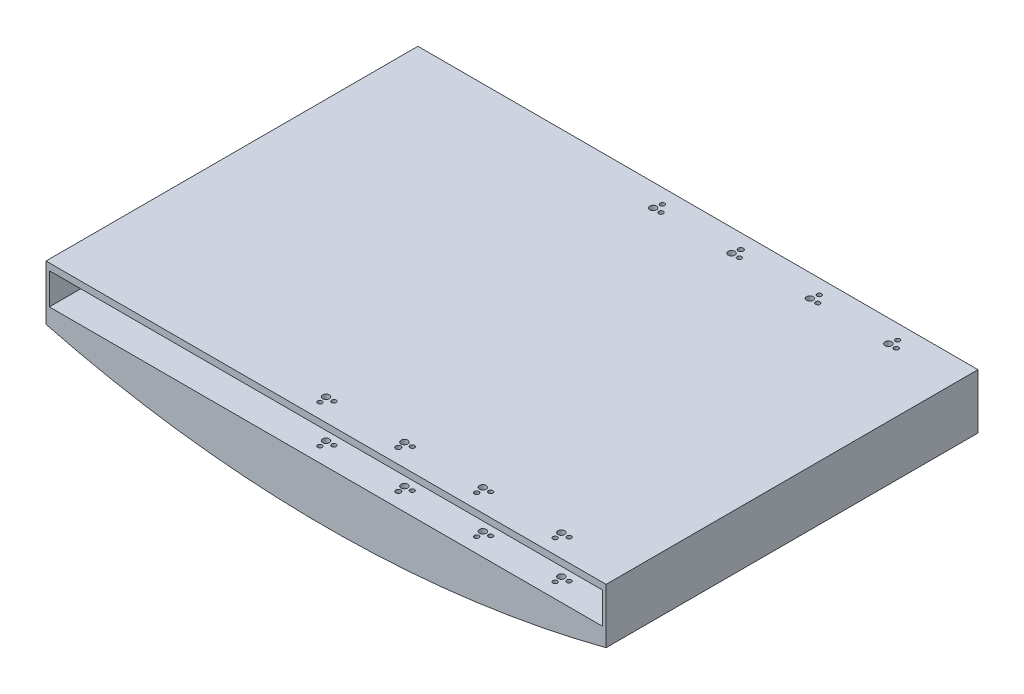
SolidWorks part; units mm, degrees
ref_plane "Front Plane" through (0, 0, 0) normal (0, 0, 1) x (1, 0, 0)
ref_plane "Top Plane" through (0, 0, 0) normal (0, 1, 0) x (1, 0, 0)
ref_plane "Right Plane" through (0, 0, 0) normal (1, 0, 0) x (0, 0, -1)
sketch "Sketch1" plane through (0, 0, 0) normal (0, 0, 1) x (1, 0, 0)
  line L2 (0, 0) -> (0, 49)
  line L3 (0, 49) -> (500, 49)
  line L4 (500, 0) -> (500, 49)
  line L9 (3, 45.5) -> (497, 45.5)
  line L10 (3, 45.5) -> (3, 12.5)
  line L11 (3, 12.5) -> (497, 12.5)
  line L12 (497, 45.5) -> (497, 12.5)
  arc A0 (0, 0) -> (500, 0) centre (250, 967.6003) ccw
  point P6 (250, -31.7747)
  dimension "D3" = 494
  dimension "D1" = 500
  dimension "D2" = 49
  dimension "D4" = 3
  dimension "D5" = 33
  dimension "D6" = 3.5
extrude "Boss-Extrude2" add sketch "Sketch1" along normal mid plane 332
sketch "Sketch6" plane through (0, 0, 0) normal (0, 0, 1) x (1, 0, 0)
  line L0 (3, 0) -> (497, 0)
  line L1 (3, 0) -> (3, -32.5581)
  line L2 (497, 0) -> (497, -32.5581)
  line L3 (3, -32.5581) -> (497, -32.5581)
  point P0 (497, 0)
  point P1 (3, 0)
extrude "Cut-Extrude2" cut sketch "Sketch6" against normal mid plane 312
sketch "Sketch7" plane through (0, 49, 0) normal (0, 1, 0) x (1, 0, 0)
  line L0 (500, -166) -> (0, -166) construction
  line L1 (0, -166) -> (0, 166) construction
  line L2 (230, -146) -> (231.3668, -152.8653) construction
  line L3 (300, -136.3) -> (300, -160.3273) construction
  line L4 (370, -134.9651) -> (370, -158.1025) construction
  line L5 (440, -134.9651) -> (440, -158.8911) construction
  line L6 (300, -146) -> (305.8829, -175.5484) construction
  line L7 (370, -146) -> (375.3706, -172.9753) construction
  line L8 (440, -146) -> (445.6513, -174.3852) construction
  line L10 (-44.4261, 0) -> (44.4261, 0) construction
  circle A0 centre (230, -146) radius 3
  circle A1 centre (300, -146) radius 3
  circle A2 centre (370, -146) radius 3
  circle A3 centre (440, -146) radius 3
  circle A8 centre (231.3668, -152.8653) radius 2
  circle A9 centre (301.3668, -152.8653) radius 2.2706
  circle A10 centre (371.3668, -152.8653) radius 2
  circle A11 centre (441.3668, -152.8653) radius 2
  circle A12 centre (237, -146) radius 2
  circle A13 centre (307, -146) radius 2
  circle A14 centre (377, -146) radius 2
  circle A15 centre (447, -146) radius 2
  circle A24 centre (440, 146) radius 3
  circle A25 centre (370, 146) radius 3
  circle A26 centre (300, 146) radius 3
  circle A27 centre (230, 146) radius 3
  circle A28 centre (441.3668, 152.8653) radius 2
  circle A29 centre (447, 146) radius 2
  circle A30 centre (371.3668, 152.8653) radius 2
  circle A31 centre (377, 146) radius 2
  circle A32 centre (307, 146) radius 2
  circle A33 centre (301.3668, 152.8653) radius 2.2706
  circle A34 centre (237, 146) radius 2
  circle A35 centre (231.3668, 152.8653) radius 2
  dimension "D1" = 6
  dimension "D2" = 6
  dimension "D3" = 6
  dimension "D4" = 6
  dimension "D10" = 4
  dimension "D18" = 4
  dimension "D19" = 4
  dimension "D21" = 4
  dimension "D22" = 4
  dimension "D25" = 4
  dimension "D26" = 4
  dimension "D5" = 20
  dimension "D6" = 230
  dimension "D7" = 70
  dimension "D8" = 70
  dimension "D9" = 70
  dimension "D11" = 7
  dimension "D12" = 11.26
  dimension "D13" = 11.26
  dimension "D14" = 11.26
  dimension "D15" = 7
  dimension "D16" = 7
  dimension "D17" = 7
  dimension "D20" = 7
  dimension "D23" = 7
  dimension "D24" = 7
  dimension "D27" = 7
sketch "Sketch8" plane through (0, 12.5, 0) normal (0, 1, 0) x (1, 0, 0)
  line L0 (3, -166) -> (497, -166)
  line L1 (3, -166) -> (3, -136)
  line L2 (497, -166) -> (497, -136)
  line L3 (3, -136) -> (497, -136)
  dimension "D1" = 30
extrude "Boss-Extrude3" add sketch "Sketch8" along normal blind 2.5
sketch "Sketch9" plane through (0, 45.5, 0) normal (0, -1, 0) x (1, 0, 0)
  line L0 (497, 166) -> (497, -166) construction
  line L1 (3, 166) -> (497, 166)
  line L2 (3, 166) -> (3, 136)
  line L3 (3, 136) -> (497, 136)
  line L4 (497, 166) -> (497, 136)
  dimension "D1" = 30
extrude "Boss-Extrude4" add sketch "Sketch9" along normal blind 2.5
sketch "Sketch10" plane through (0, 45.5, 0) normal (0, -1, 0) x (1, 0, 0)
  line L0 (497, 136) -> (497, -166) construction
  line L1 (3, -166) -> (497, -166)
  line L2 (3, -166) -> (3, -136)
  line L3 (3, -136) -> (497, -136)
  line L4 (497, -166) -> (497, -136)
  dimension "D1" = 30
extrude "Boss-Extrude5" add sketch "Sketch10" along normal blind 2.5
sketch "Sketch11" plane through (0, 12.5, 0) normal (0, 1, 0) x (1, 0, 0)
  line L0 (3, -136) -> (3, 166) construction
  line L1 (497, 166) -> (3, 166)
  line L2 (497, 166) -> (497, 136)
  line L3 (497, 136) -> (3, 136)
  line L4 (3, 166) -> (3, 136)
  dimension "D1" = 30
extrude "Boss-Extrude6" add sketch "Sketch11" along normal blind 2.5
extrude "Cut-Extrude3" cut sketch "Sketch7" against normal through all both and the other way through all
